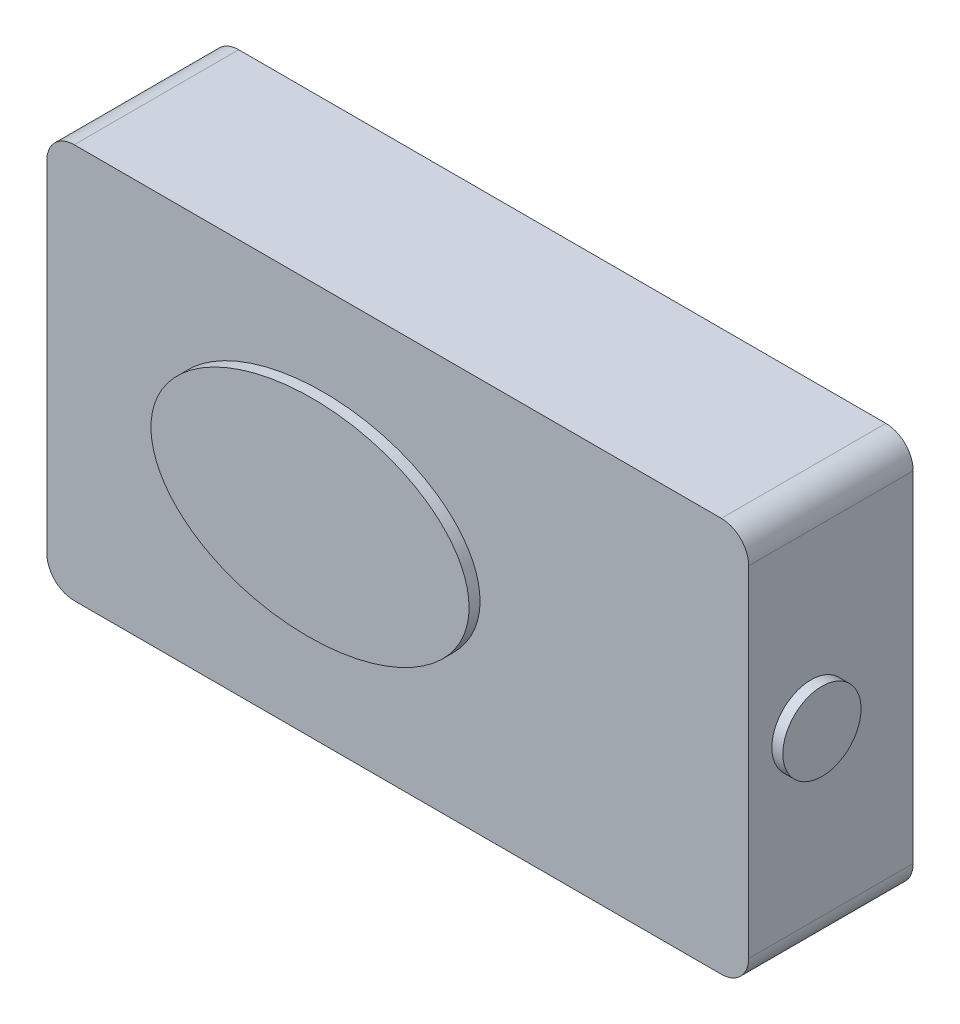
SolidWorks part; units mm, degrees
ref_plane "Front Plane" through (0, 0, 0) normal (0, 0, 1) x (1, 0, 0)
ref_plane "Top Plane" through (0, 0, 0) normal (0, 1, 0) x (1, 0, 0)
ref_plane "Right Plane" through (0, 0, 0) normal (1, 0, 0) x (0, 0, -1)
sketch "Sketch1" plane through (0, 0, 0) normal (0, 0, 1) x (1, 0, 0)
  line L1 (-29.6895, 17.9061) -> (34.3105, 17.9061)
  line L2 (-29.6895, 17.9061) -> (-29.6895, -18.0939)
  line L3 (-29.6895, -18.0939) -> (34.3105, -18.0939)
  line L4 (34.3105, 17.9061) -> (34.3105, -18.0939)
  dimension "D1" = 64
  dimension "D2" = 36
extrude "Boss-Extrude1" add sketch "Sketch1" along normal blind 15
fillet "Fillet1" radius 2.5 4 edges at (-29.6895, -18.0939, 7.5) (34.3105, -18.0939, 7.5) (34.3105, 17.9061, 7.5) (-29.6895, 17.9061, 7.5)
sketch "Sketch2" plane through (0, 0, 15) normal (0, 0, 1) x (1, 0, 0)
  line L0 (-29.6895, 15.4061) -> (-29.6895, -15.5939) construction
  ellipse E0 centre (-4.6895, 0.2372) end of major axis (9.8105, 0.4744) minor radius 9.5
  dimension "D1" = 25
extrude "Boss-Extrude2" add sketch "Sketch2" along normal blind 1
sketch "Sketch3" plane through (34.3105, 0, 0) normal (1, 0, 0) x (0, 0, -1)
  circle A0 centre (-9.3251, 0) radius 3.5637
extrude "Boss-Extrude3" add sketch "Sketch3" along normal blind 1
